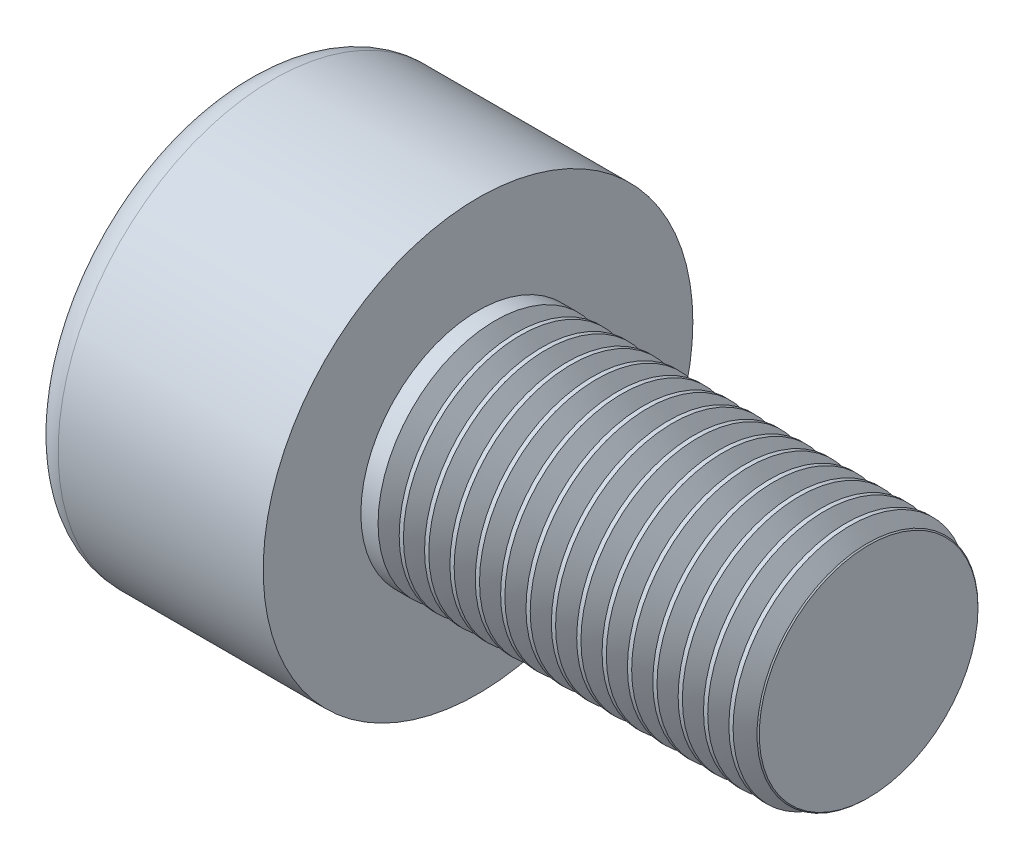
SolidWorks part; units mm, degrees
ref_plane "Front" through (0, 0, 0) normal (0, 0, 1) x (1, 0, 0)
ref_plane "Top" through (0, 0, 0) normal (0, 1, 0) x (1, 0, 0)
ref_plane "Right" through (0, 0, 0) normal (1, 0, 0) x (0, 0, -1)
sketch "Sketch1" plane through (0, 0, 0) normal (1, 0, 0) x (0, 0, -1)
  circle A0 centre (0, 0) radius 2.75
  dimension "dk" = 5.5
extrude "BaseHead" add sketch "Sketch1" along normal blind 3
sketch "Sketch2" plane through (3, 0, 0) normal (1, 0, 0) x (0, 0, -1)
  circle A0 centre (0, 0) radius 1.5
  dimension "d" = 3
extrude "BaseBody" add sketch "Sketch2" along normal blind 5
cosmetic thread "ThreadCosmetic1" [suppressed] parameters "b"=5, "D2"=2.459
sketch "Sketch3" plane through (0, 0, 0) normal (1, 0, 0) x (0, 0, -1)
  line L1 (1.4434, 0) -> (0.7217, 1.25)
  line L2 (0.7217, 1.25) -> (-0.7217, 1.25)
  line L3 (-0.7217, 1.25) -> (-1.4434, 0)
  line L4 (-1.4434, 0) -> (-0.7217, -1.25)
  line L5 (-0.7217, -1.25) -> (0.7217, -1.25)
  line L6 (0.7217, -1.25) -> (1.4434, 0)
  circle A0 centre (0, 0) radius 1.25 construction
  dimension "s" = 2.5
  dimension "e" = 2.8868
extrude "HexagonSocket" cut sketch "Sketch3" along normal blind 1.3
sketch "Sketch4" plane through (-4.1961, 0.75, 0) normal (0, 0, 1) x (-1, 0, 0)
  line L0 (-5.4961, 2) -> (-6.2178, 0.75)
  line L2 (-6.2178, 0.75) -> (-5.4961, 0.75)
  line L3 (-5.4961, 0.75) -> (-5.4961, 2)
  line L4 (-5.0351, 0.75) -> (0.839, 0.75) construction
  line L5 (-12.1961, 0.75) -> (-7.1961, 0.75) construction
  line L6 (-7.1961, 0.75) -> (-4.1961, 0.75) construction
  dimension "m" = 60
revolve "Cut-Revolve1" cut sketch "Sketch4" angle 360 about L4
fillet "HeadFillet" [suppressed] radius 0.1
fillet "TopFillet" radius 0.375 1 edges at (0, 0, -2.75)
chamfer "Chamfer1" distance 0.1 angle 45 1 edges at (8, 0, -1.5)
sketch "Sketch5" plane through (0, 0, 0) normal (0, 0, 1) x (1, 0, 0)
  line L0 (7.9, 1.2657) -> (8.0352, 1.5)
  line L1 (8.0352, 1.5) -> (8.0352, 1.7705)
  line L2 (8.0352, 1.7705) -> (7.7647, 1.7705)
  line L3 (7.7647, 1.7705) -> (7.7647, 1.5)
  line L4 (7.7647, 1.5) -> (7.9, 1.2657)
  line L5 (0, 0) -> (7.8886, 0) construction
  line L6 (7.9, -1.5) -> (7.9, 1.5) construction
  dimension "D1" = 3
  dimension "D2" = 0.2705
revolve "Cut-Revolve10" cut sketch "Sketch5" angle 360 about L5
pattern_linear "LPattern10" count 15 spacing 0.3246 along (-1, 0, 0) of "Cut-Revolve10"
equation "\"r1@TopFillet\" = \"d@Sketch2\" / 8"
equation "\"D1@Chamfer1\" = \"r@HeadFillet\""
equation "\"D1@Sketch5\" = \"d@Sketch2\""
equation "\"D2@Sketch5\" =  ( \"d@Sketch2\" - \"D2@ThreadCosmetic1\" )  / 2"
equation "\"D3@LPattern10\" = \"D2@Sketch5\" * 1.2"
equation "\"D1@LPattern10\" = \"b@ThreadCosmetic1\" / \"D3@LPattern10\""
